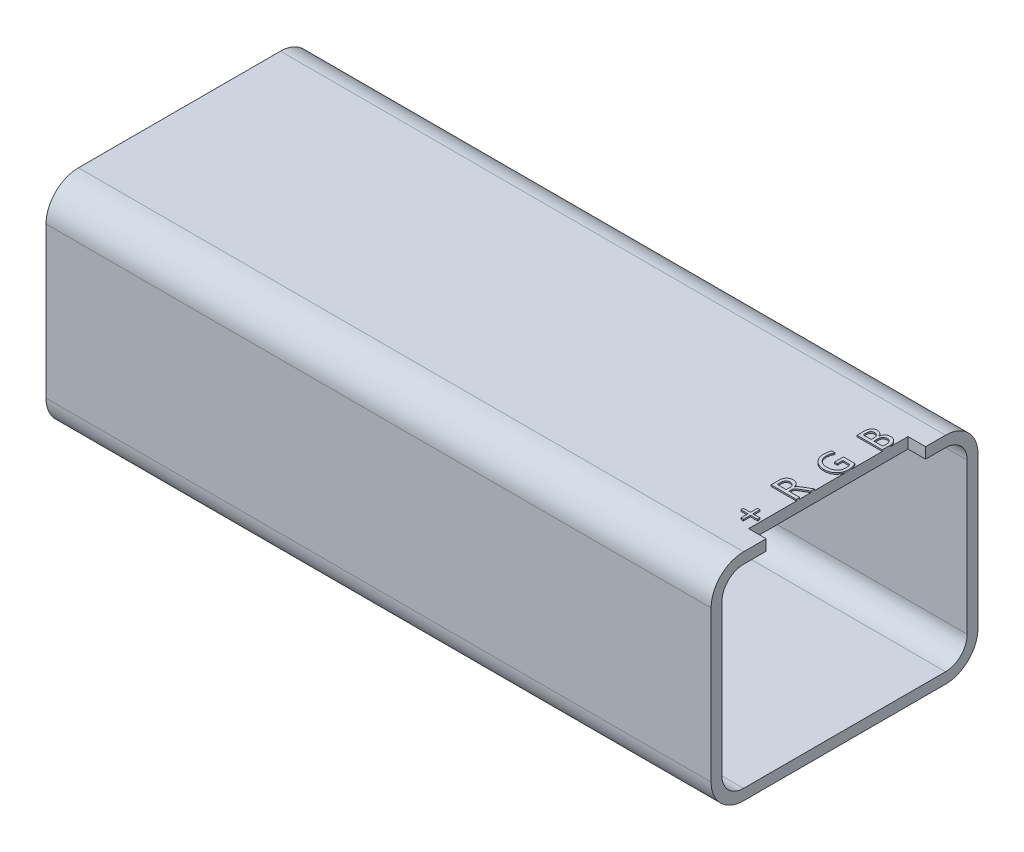
SolidWorks part; units mm, degrees
ref_plane "前视基准面" through (0, 0, 0) normal (0, 0, 1) x (1, 0, 0)
ref_plane "上视基准面" through (0, 0, 0) normal (0, 1, 0) x (1, 0, 0)
ref_plane "右视基准面" through (0, 0, 0) normal (1, 0, 0) x (0, 0, -1)
sketch "草图3" plane through (29.1, 0, 0) normal (1, 0, 0) x (0, 0, -1)
  line L18 (-1, 0) -> (-1, -2.5) construction
  line L19 (0, -3.5) -> (28, -3.5) construction
  line L20 (29, -2.5) -> (29, 0) construction
  line L21 (29, 0) -> (29, 19.4)
  line L22 (-1, 19.4) -> (-1, 0)
  line L23 (29, 19.4) -> (-1, 19.4)
  line L24 (29, 0) -> (29, 18.4) construction
  line L25 (-1, 18.4) -> (-1, 0) construction
  line L26 (28, 19.4) -> (0, 19.4) construction
  line L27 (27, -2.5) -> (1, -2.5) construction
  line L29 (-3, 0) -> (-3, -2.5)
  line L30 (0, -5.5) -> (28, -5.5)
  line L31 (31, -2.5) -> (31, 0)
  line L32 (31, 0) -> (31, 18.4)
  line L33 (28, 21.4) -> (0, 21.4)
  line L34 (-3, 18.4) -> (-3, 0)
  line L35 (-4.5, 0) -> (-4.5, -2.5)
  line L36 (0, -7) -> (28, -7)
  line L37 (32.5, -2.5) -> (32.5, 0)
  line L38 (32.5, 0) -> (32.5, 18.4)
  line L39 (28, 22.9) -> (0, 22.9)
  line L40 (-4.5, 18.4) -> (-4.5, 0)
  arc A0 (0, -3.5) -> (-1, -2.5) centre (0, -2.5) cw construction
  arc A1 (28, -3.5) -> (29, -2.5) centre (28, -2.5) ccw construction
  arc A2 (29, 18.4) -> (28, 19.4) centre (28, 18.4) ccw construction
  arc A3 (0, 19.4) -> (-1, 18.4) centre (0, 18.4) ccw construction
  arc A4 (0, -5.5) -> (-3, -2.5) centre (0, -2.5) cw
  arc A5 (28, -5.5) -> (31, -2.5) centre (28, -2.5) ccw
  arc A6 (31, 18.4) -> (28, 21.4) centre (28, 18.4) ccw
  arc A7 (0, 21.4) -> (-3, 18.4) centre (0, 18.4) ccw
  arc A8 (0, -7) -> (-4.5, -2.5) centre (0, -2.5) cw
  arc A9 (28, -7) -> (32.5, -2.5) centre (28, -2.5) ccw
  arc A10 (32.5, 18.4) -> (28, 22.9) centre (28, 18.4) ccw
  arc A11 (0, 22.9) -> (-4.5, 18.4) centre (0, 18.4) ccw
  dimension "D3" = 1
  dimension "D2" = 1
  dimension "D1" = 1
  dimension "D4" = 2
  dimension "D5" = 1.5
extrude "凸台-拉伸1" add sketch "草图3" against normal offset from surface 20 and the other way up to surface (14 mm away)
sketch "草图5" plane through (43.1, 0, 0) normal (1, 0, 0) x (0, 0, -1)
  line L6 (25.2327, 21) -> (25.2327, 22.9) construction
  line L7 (3.1327, 22.9) -> (25.2327, 22.9)
  line L8 (3.1327, 22.9) -> (3.1327, 21.4)
  line L9 (3.1327, 21.4) -> (25.2327, 21.4)
  line L10 (25.2327, 22.9) -> (25.2327, 21.4)
  line L11 (0, 21.4) -> (28, 21.4) construction
extrude "切除-拉伸1" cut sketch "草图5" against normal offset from surface (2.4301 mm away) 1
sketch "草图6" plane through (0, 22.9, 0) normal (0, 1, 0) x (1, 0, 0)
  text T0 "+  R  G  B" font "@Microsoft YaHei UI" height 3.5
extrude "凸台-拉伸2" add sketch "草图6" along normal blind 0.2
